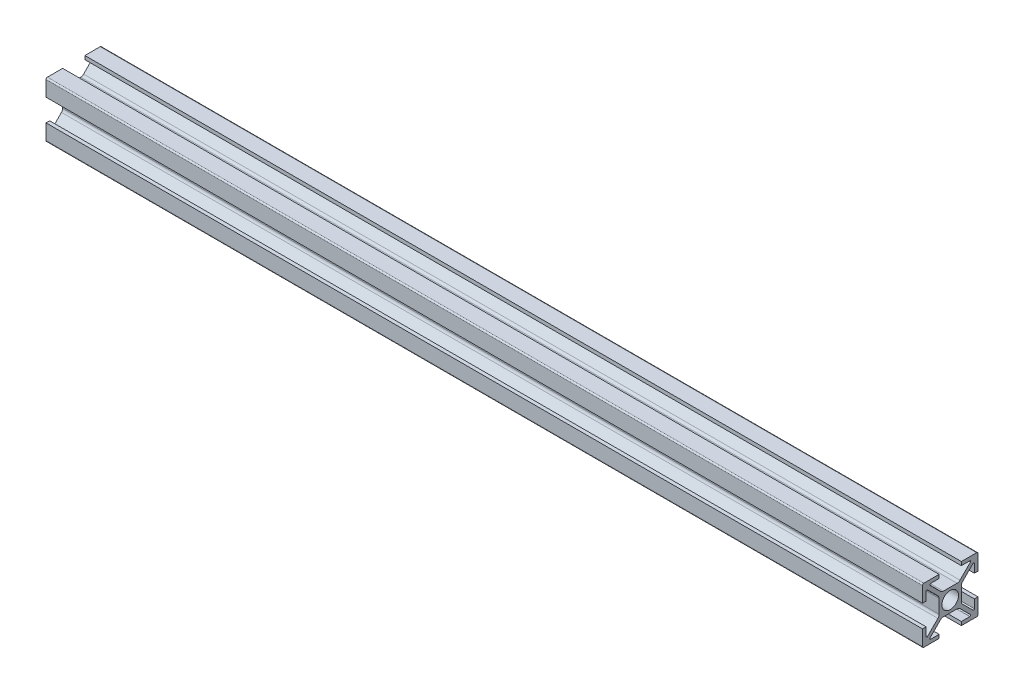
SolidWorks part; units mm, degrees
material "6061 Alloy"
ref_plane "Plano frontal" through (0, 0, 0) normal (0, 0, 1) x (1, 0, 0)
ref_plane "Plano superior" through (0, 0, 0) normal (0, 1, 0) x (1, 0, 0)
ref_plane "Plano direito" through (0, 0, 0) normal (1, 0, 0) x (0, 0, -1)
sketch "Esboço1" plane through (0, 0, 0) normal (0, 0, 1) x (1, 0, 0)
  line L0 (0, 0) -> (315.6, 0)
  dimension "D1" = 315.6
other "Quadrado PF20-01 - PERFIL 2020 BÁSICO(1)"
ref_plane "Plano1" through (0, 0, 0) normal (1, 0, 0) x (0, 1, 0)
sketch "Sketch1" plane through (0, 0, 0) normal (1, 0, 0) x (0, 1, 0)
  line L0 (8.1879, -7.2686) -> (4.4393, -3.5201)
  line L1 (4, -2.4594) -> (4, 2.4594)
  line L2 (4.4393, 3.5201) -> (8.1879, 7.2686)
  line L3 (8.7, 7.0565) -> (8.7, 4)
  line L4 (8.7, 4) -> (10, 4)
  line L5 (10, 4) -> (10, 9.5)
  line L6 (9.5, 10) -> (4, 10)
  line L7 (4, 10) -> (4, 8.7)
  line L8 (4, 8.7) -> (7.0565, 8.7)
  line L9 (7.2686, 8.1879) -> (3.5201, 4.4393)
  line L10 (2.4594, 4) -> (-2.4594, 4)
  line L11 (-3.5201, 4.4393) -> (-7.2686, 8.1879)
  line L12 (-7.0565, 8.7) -> (-4, 8.7)
  line L13 (-4, 8.7) -> (-4, 10)
  line L14 (-4, 10) -> (-9.5, 10)
  line L15 (-10, 9.5) -> (-10, 4)
  line L16 (-10, 4) -> (-8.7, 4)
  line L17 (-8.7, 4) -> (-8.7, 7.0565)
  line L18 (-8.1879, 7.2686) -> (-4.4393, 3.5201)
  line L19 (-4, 2.4594) -> (-4, -2.4594)
  line L20 (-4.4393, -3.5201) -> (-8.1879, -7.2686)
  line L21 (-8.7, -7.0565) -> (-8.7, -4)
  line L22 (-8.7, -4) -> (-10, -4)
  line L23 (-10, -4) -> (-10, -9.5)
  line L24 (-9.5, -10) -> (-4, -10)
  line L25 (-4, -10) -> (-4, -8.7)
  line L26 (-4, -8.7) -> (-7.0565, -8.7)
  line L27 (-7.2686, -8.1879) -> (-3.5201, -4.4393)
  line L28 (-2.4594, -4) -> (2.4594, -4)
  line L29 (3.5201, -4.4393) -> (7.2686, -8.1879)
  line L30 (7.0565, -8.7) -> (4, -8.7)
  line L31 (4, -8.7) -> (4, -10)
  line L32 (4, -10) -> (9.5, -10)
  line L33 (10, -9.5) -> (10, -4)
  line L34 (10, -4) -> (8.7, -4)
  line L35 (8.7, -4) -> (8.7, -7.0565)
  circle A0 centre (0, 0) radius 3
  arc A1 (8.1879, -7.2686) -> (8.7, -7.0565) centre (8.4, -7.0565) ccw
  arc A2 (4, -2.4594) -> (4.4393, -3.5201) centre (5.5, -2.4594) ccw
  arc A3 (4.4393, 3.5201) -> (4, 2.4594) centre (5.5, 2.4594) ccw
  arc A4 (8.7, 7.0565) -> (8.1879, 7.2686) centre (8.4, 7.0565) ccw
  arc A5 (10, 9.5) -> (9.5, 10) centre (9.5, 9.5) ccw
  arc A6 (7.2686, 8.1879) -> (7.0565, 8.7) centre (7.0565, 8.4) ccw
  arc A7 (2.4594, 4) -> (3.5201, 4.4393) centre (2.4594, 5.5) ccw
  arc A8 (-3.5201, 4.4393) -> (-2.4594, 4) centre (-2.4594, 5.5) ccw
  arc A9 (-7.0565, 8.7) -> (-7.2686, 8.1879) centre (-7.0565, 8.4) ccw
  arc A10 (-9.5, 10) -> (-10, 9.5) centre (-9.5, 9.5) ccw
  arc A11 (-8.1879, 7.2686) -> (-8.7, 7.0565) centre (-8.4, 7.0565) ccw
  arc A12 (-4, 2.4594) -> (-4.4393, 3.5201) centre (-5.5, 2.4594) ccw
  arc A13 (-4.4393, -3.5201) -> (-4, -2.4594) centre (-5.5, -2.4594) ccw
  arc A14 (-8.7, -7.0565) -> (-8.1879, -7.2686) centre (-8.4, -7.0565) ccw
  arc A15 (-10, -9.5) -> (-9.5, -10) centre (-9.5, -9.5) ccw
  arc A16 (-7.2686, -8.1879) -> (-7.0565, -8.7) centre (-7.0565, -8.4) ccw
  arc A17 (-2.4594, -4) -> (-3.5201, -4.4393) centre (-2.4594, -5.5) ccw
  arc A18 (3.5201, -4.4393) -> (2.4594, -4) centre (2.4594, -5.5) ccw
  arc A19 (7.0565, -8.7) -> (7.2686, -8.1879) centre (7.0565, -8.4) ccw
  arc A20 (9.5, -10) -> (10, -9.5) centre (9.5, -9.5) ccw
  point P0 (0, 10)
  point P1 (-10, 10)
  point P2 (10, 10)
  point P3 (10, 0)
  point P4 (10, -10)
  point P5 (0, -10)
  point P6 (-10, -10)
  point P7 (-10, 0)
  point P8 (0, 0)
  point P87 (0, 0)
  dimension "D2" = 20
  dimension "D3" = 5.5
  dimension "D8" = 45
  dimension "D9" = 8
  dimension "D10" = 8
